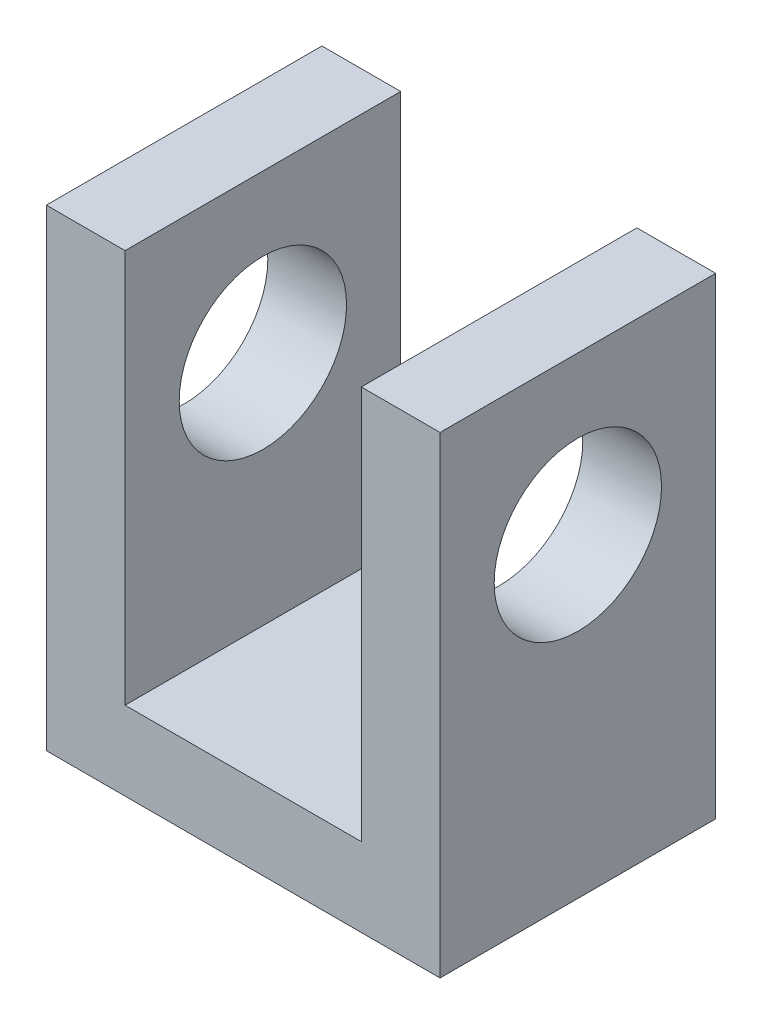
SolidWorks part; units mm, degrees
ref_plane "Front Plane" through (0, 0, 0) normal (0, 0, 1) x (1, 0, 0)
ref_plane "Top Plane" through (0, 0, 0) normal (0, 1, 0) x (1, 0, 0)
ref_plane "Right Plane" through (0, 0, 0) normal (1, 0, 0) x (0, 0, -1)
sketch "Sketch1" plane through (0, 0, 0) normal (0, 1, 0) x (1, 0, 0)
  line L1 (0, 0) -> (10, 0)
  line L2 (0, 0) -> (0, 7)
  line L3 (0, 7) -> (10, 7)
  line L4 (10, 0) -> (10, 7)
  dimension "D1" = 10
  dimension "D2" = 7
extrude "Boss-Extrude1" add sketch "Sketch1" along normal blind 12
sketch "Sketch2" plane through (0, 12, 0) normal (0, 1, 0) x (1, 0, 0)
  line L0 (5, 0) -> (5, 7) construction
  line L1 (0, 0) -> (10, 0) construction
  line L2 (10, 7) -> (0, 7) construction
  line L4 (5, 7) -> (8, 7)
  line L5 (5, 7) -> (5, 0)
  line L6 (5, 0) -> (8, 0)
  line L7 (8, 7) -> (8, 0)
  line L8 (5, 7) -> (2, 7)
  line L9 (5, 7) -> (5, 0)
  line L10 (5, 0) -> (2, 0)
  line L11 (2, 7) -> (2, 0)
  line M4 (0, 0) -> (10, 0)
  line M6 (10, 7) -> (0, 7)
  dimension "D1" = 3
  dimension "D2" = 3
extrude "Cut-Extrude1" cut sketch "Sketch2" against normal blind 10 contours L11 L5 M6 M4 | L7 L5 M6 M4
sketch "Sketch3" plane through (10, 0, 0) normal (1, 0, 0) x (0, 0, -1)
  line L0 (0, 2) -> (7, 2)
  line L1 (0, 12) -> (0, 0) construction
  line L2 (7, 12) -> (7, 0) construction
  line L3 (0, 0) -> (7, 0) construction
  circle A0 centre (3.5, 8) radius 2.125
  dimension "D2" = 6
  dimension "D1" = 2
extrude "Cut-Extrude2" cut sketch "Sketch3" against normal through all contours A0
